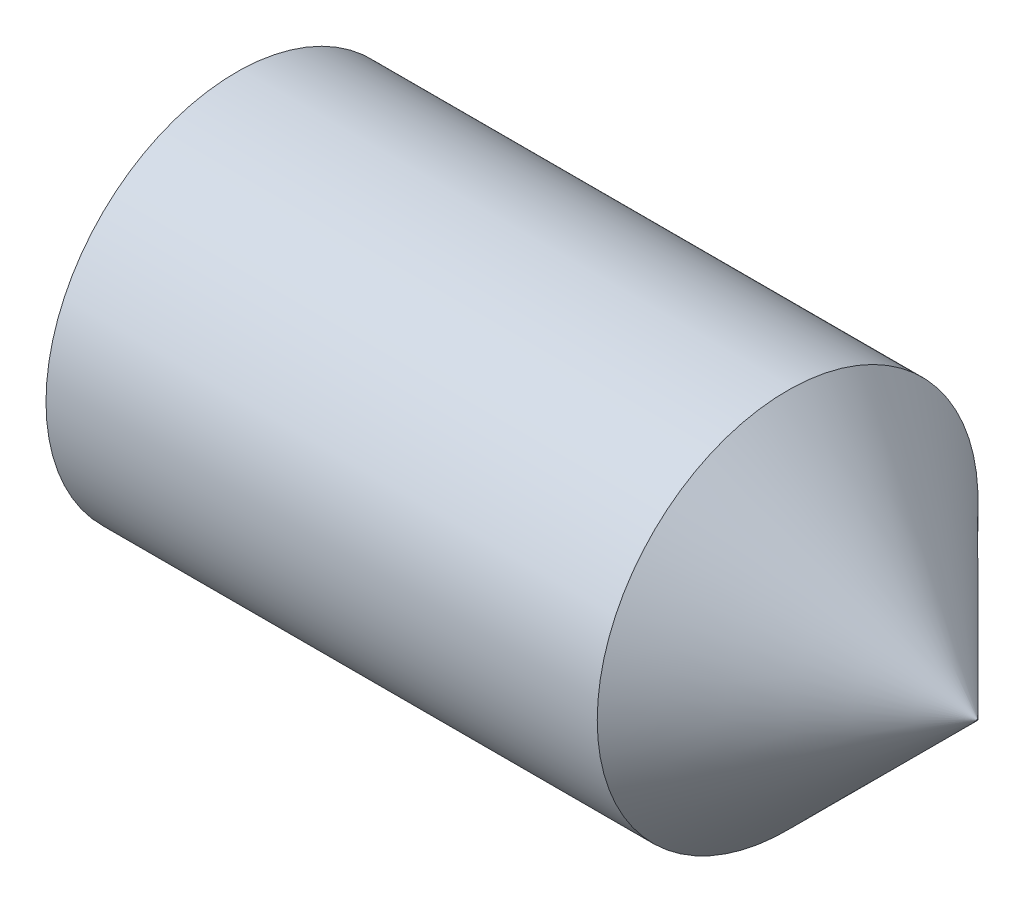
SolidWorks part; units mm, degrees
revolve "BaseBody" add sketch "BodySke" angle 360 about L5
sketch "BodySke" plane through (0, 0, 0) normal (0, 0, 1) x (1, 0, 0)
  line L0 (0, 0) -> (0, 1.2195)
  line L1 (0, 1.2195) -> (0.1619, 1.5)
  line L2 (0.1619, 1.5) -> (4.505, 1.5)
  line L3 (6, 0) -> (6, 0.005)
  line L4 (6, 0) -> (0, 0)
  line L5 (-12.7, 0) -> (88.9, 0) construction
  line L6 (6, 0.005) -> (4.505, 1.5)
  line L7 (0.5, 15.875) -> (0.5, -3.175) construction
  line L8 (0, -1.2195) -> (0.1619, -1.5) construction
  line L9 (6, -0.005) -> (4.505, -1.5) construction
  dimension "Diameter" = 3
  dimension "Drive_ch_ang" = 60
  dimension "Minor_dia" = 2.439
  dimension "Advance" = 0.5
  dimension "Length" = 6
  dimension "Tip_dia" = 0.01
  dimension "Cone_ang" = 90
cosmetic thread "ThreadCosmetic" [suppressed] parameters "Thread_minor"=2.439
ref_plane "Plane1" through (0, 0, 0) normal (0, 0, 1) x (1, 0, 0)
ref_plane "Plane2" through (0, 0, 0) normal (0, 1, 0) x (1, 0, 0)
ref_plane "Plane3" through (0, 0, 0) normal (1, 0, 0) x (0, 0, -1)
sketch "Sketch2" plane through (0, 0, 0) normal (-1, 0, 0) x (0, 0, 1)
  line L0 (0.433, 0.75) -> (-0.433, 0.75)
  line L1 (-0.433, 0.75) -> (-0.866, 0)
  line L2 (0.433, 0.75) -> (0.866, 0)
  line L3 (0.433, -0.75) -> (0.866, 0)
  line L4 (0.433, -0.75) -> (-0.433, -0.75)
  line L5 (-0.433, -0.75) -> (-0.866, 0)
  dimension "Hex_size" = 1.5
  dimension "D2" = 0.75
  dimension "D3" = 0.75
extrude "Hex" cut sketch "Sketch2" against normal blind 2.1
sketch "Sketch4" [suppressed] plane through (0, 4.7709, -0.5249) normal (-1, 0, 0) x (0, 0, 1)
  line L0 (0.5249, -4.7709) -> (10.6976, -4.7709)
  line L1 (0.5249, -4.7709) -> (6.6732, -1.2211) construction
  line L2 (0.5249, -4.7709) -> (5.6112, 4.0389)
  line L3 (8.9666, -2.6687) -> (10.2861, -1.9069)
  line L4 (6.5663, 1.4888) -> (7.8858, 2.2506)
  arc A0 (8.9666, -2.6687) -> (6.5663, 1.4888) centre (0.5249, -4.7709) ccw
  arc A1 (10.6976, -4.7709) -> (10.2861, -1.9069) centre (0.5249, -4.7709) ccw
  arc A2 (5.6112, 4.0389) -> (7.8858, 2.2506) centre (0.5249, -4.7709) cw
  circle A3 centre (0.5249, -4.7709) radius 8.6995 construction
  circle A4 centre (0.5249, -4.7709) radius 10.1727 construction
  dimension "Spline_n_dim" = 1.295
  dimension "Spline_m_dim" = 1.575
  dimension "D1" = 30
  dimension "Spline_a_dim" = 60
  dimension "Spline_p_dim" = 0.356
  dimension "D3" = 0.178
extrude "Spline6" [suppressed] cut sketch "Sketch4" against normal blind 1.2
pattern_circular "CirPattern1" [suppressed] count 6 every 60 about axis through (-12.7, 0, 0) along (1, 0, 0)
sketch "Sketch5" [suppressed] plane through (0, 1.4735, 6.925) normal (-1, 0, 0) x (0, 0, 1)
  line L0 (-6.925, -1.4735) -> (3.2477, -1.4735)
  line L1 (-6.925, -1.4735) -> (-1.9049, 3.5466) construction
  line L2 (-6.925, -1.4735) -> (-6.925, 8.6992)
  line L3 (0.9237, 2.9807) -> (1.7623, 3.8193)
  line L4 (-2.4708, 6.3752) -> (-1.6322, 7.2139)
  line L5 (-2.4708, 6.3752) -> (0.9237, 2.9807)
  arc A1 (3.2477, -1.4735) -> (1.7623, 3.8193) centre (-6.925, -1.4735) ccw
  arc A2 (-6.925, 8.6992) -> (-1.6322, 7.2139) centre (-6.925, -1.4735) cw
  circle A3 centre (-6.925, -1.4735) radius 8.6995 construction
  circle A4 centre (-6.925, -1.4735) radius 10.1727 construction
  dimension "Spline_n_dim" = 1.295
  dimension "Spline_m_dim" = 1.575
  dimension "Spline_p_dim" = 0.356
  dimension "D3" = 0.178
  dimension "D1" = 45
  dimension "Spline_a_dim" = 90
extrude "Spline4" [suppressed] cut sketch "Sketch5" against normal blind 1.2
pattern_circular "CirPattern2" [suppressed] count 4 every 90 about axis through (-12.7, 0, 0) along (1, 0, 0)
sketch "ThdSchSke" [suppressed] plane through (0, 0, 0) normal (0, 0, 1) x (1, 0, 0)
  line L0 (0.9515, -10.352) -> (-0.2025, -12)
  line L1 (0.9515, -10.352) -> (2.1054, -12)
  line L2 (2.1054, -12) -> (2.1054, -15)
  line L3 (-3.175, 0) -> (5.1513, 0) construction
  line L4 (0.9515, 12) -> (0.9515, -12) construction
  line L5 (2.1054, -15) -> (-0.2025, -15)
  line L6 (-0.2025, -15) -> (-0.2025, -12)
  dimension "Thread_minor" = 2.439
  dimension "Diameter" = 3
revolve "ThreadSchematic" [suppressed] cut sketch "ThdSchSke" angle 360 about L3
pattern_linear "ThdSchPat" [suppressed]
equation "\"D2@Sketch2\" = \"Hex_size@Sketch2\" / 2"
equation "\"D3@Sketch2\" = \"Hex_size@Sketch2\" / 2"
equation "\"Thread_minor@ThreadCosmetic\" = \"Minor_dia@BodySke\""
equation "\"D1@Sketch4\" = \"Spline_a_dim@Sketch4\" / 2"
equation "\"D3@Sketch4\" = \"Spline_p_dim@Sketch4\" / 2"
equation "\"D2@CirPattern1\" = \"Spline_a_dim@Sketch4\""
equation "\"Num_teeth@CirPattern1\" = 360 / \"D2@CirPattern1\""
equation "\"Spline_a_dim@Sketch5\" = 90"
equation "\"Spline_p_dim@Sketch5\" = \"Spline_p_dim@Sketch4\""
equation "\"Spline_m_dim@Sketch5\" = \"Spline_m_dim@Sketch4\""
equation "\"Spline_n_dim@Sketch5\" = \"Spline_n_dim@Sketch4\""
equation "\"D1@Sketch5\" = \"Spline_a_dim@Sketch5\" / 2"
equation "\"D3@Sketch5\" = \"Spline_p_dim@Sketch5\" / 2"
equation "\"Key_eng@Spline4\" = \"Key_eng@Spline6\""
equation "\"Thread_minor@ThdSchSke\" = \"Thread_minor@ThreadCosmetic\""
equation "\"Diameter@ThdSchSke\" = \"Diameter@BodySke\""
equation "\"Overcut@ThdSchSke\" = \"Diameter@BodySke\" * 1.25"
equation "\"Num_threads@ThdSchPat\" = int( (\"Length@BodySke\" - ( ( ( \"Diameter@BodySke\" - \"Minor_dia@BodySke\" ) * 0.5 ) / tan( \"Drive_ch_ang@BodySke\" * 0.017453292 ) ) - ( ( \"Diameter@BodySke\" * 0.5 ) / tan( \"Cone_ang@BodySke\" * 0.008726646 ) ) ) / \"Advance@BodySke\" + 0.999 )  + 1"
equation "\"Num_threads@ThdSchPat\" = int( (\"Length@BodySke\" - ( ( ( \"Diameter@BodySke\" - \"Minor_dia@BodySke\" ) * 0.5 ) / tan( \"Drive_ch_ang@BodySke\" * 0.017453292 ) ) - ( (( \"Diameter@BodySke\" - \"Tip_dia@BodySke\") * 0.5 ) / tan( \"Cone_ang@BodySke\" * 0.008726646 ) ) ) / \"Advance@BodySke\" + 0.999 )  + 1"
equation "\"Advance@ThdSchPat\" = (\"Length@BodySke\" - ( ( ( \"Diameter@BodySke\" - \"Minor_dia@BodySke\" ) * 0.5 ) / tan( \"Drive_ch_ang@BodySke\" * 0.017453292 ) ) - ( ( \"Diameter@BodySke\" * 0.5 ) / tan( \"Cone_ang@BodySke\" * 0.008726646 ) ) ) /  (\"Num_threads@ThdSchPat\" - 1) 'relax it"
equation "\"Advance@ThdSchPat\" = (\"Length@BodySke\" - ( ( ( \"Diameter@BodySke\" - \"Minor_dia@BodySke\" ) * 0.5 ) / tan( \"Drive_ch_ang@BodySke\" * 0.017453292 ) ) - ( ( (\"Diameter@BodySke\" - \"Tip_dia@BodySke\") * 0.5 ) / tan( \"Cone_ang@BodySke\" * 0.008726646 ) ) ) /  (\"Num_threads@ThdSchPat\" - 1) 'relax it"
equation "' \"Num_threads@ThdSchPat\" = \"Num_threads@ThdSchPat\" - sgn( \"Num_threads@ThdSchPat\" - 1) '---chamfered tips only---"
